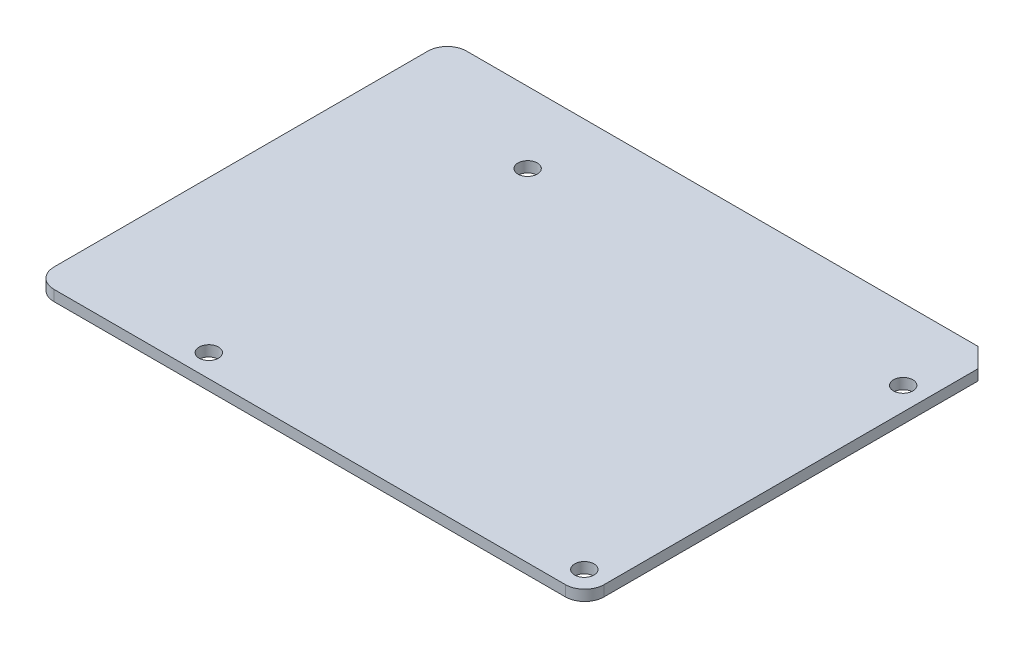
SolidWorks part; units mm, degrees
ref_plane "Front Plane" through (0, 0, 0) normal (0, 0, 1) x (1, 0, 0)
ref_plane "Top Plane" through (0, 0, 0) normal (0, 1, 0) x (1, 0, 0)
ref_plane "Right Plane" through (0, 0, 0) normal (1, 0, 0) x (0, 0, -1)
sketch "Sketch2" plane through (0, 0, 0) normal (0, 1, 0) x (1, 0, 0)
  line L1 (-42.57, -31.93) -> (42.57, -31.93)
  line L2 (-42.57, -31.93) -> (-42.57, 31.93)
  line L3 (-42.57, 31.93) -> (42.57, 31.93)
  line L4 (42.57, -31.93) -> (42.57, 31.93)
  line L5 (-42.57, -31.93) -> (42.57, 31.93) construction
  line L6 (-42.57, 31.93) -> (42.57, -31.93) construction
  line L7 (39.01, -28.43) -> (-19.11, -28.43) construction
  line L8 (39.01, -28.43) -> (39.01, 20.91) construction
  line L9 (39.01, 20.91) -> (-19.11, 20.91) construction
  line L10 (-19.11, -28.43) -> (-19.11, 20.91) construction
  line L11 (39.01, -28.43) -> (-19.11, 20.91) construction
  line L12 (39.01, 20.91) -> (-19.11, -28.43) construction
  circle A0 centre (-19.11, 20.91) radius 1.5
  circle A1 centre (39.01, 20.91) radius 1.5
  circle A2 centre (39.01, -28.43) radius 1.5
  circle A3 centre (-19.11, -28.43) radius 1.5
  point P0 (0, 0)
  point P6 (9.95, -3.76)
  dimension "D7" = 3
  dimension "D1" = 3.56
  dimension "D2" = 3.5
  dimension "D3" = 23.46
  dimension "D4" = 11.02
  dimension "D5" = 85.14
  dimension "D6" = 63.86
extrude "Boss-Extrude1" add sketch "Sketch2" along normal mid plane 1.65
fillet "Fillet1" radius 3 3 edges at (-42.57, 0, -31.93) (-42.57, 0, 31.93) (42.57, 0, 31.93)
chamfer "Chamfer1" distance 3 angle 45 1 edges at (42.57, 0, -31.93)
sketch "Sketch3" plane through (0, 0.825, 0) normal (0, 1, 0) x (1, 0, 0)
  line L0 (42.57, -28.93) -> (42.57, 28.93) construction
  line L1 (42.57, -18.93) -> (29.57, -18.93)
  line L2 (42.57, -18.93) -> (42.57, -8.93)
  line L3 (42.57, -8.93) -> (29.57, -8.93)
  line L4 (29.57, -18.93) -> (29.57, -8.93)
  line L5 (-39.57, -31.93) -> (39.57, -31.93) construction
  line L6 (29.57, -2.93) -> (29.57, 2.07)
  line L7 (42.57, -2.93) -> (37.57, -2.93)
  line L8 (42.57, -2.93) -> (42.57, 2.07)
  line L9 (42.57, 2.07) -> (37.57, 2.07)
  line L10 (37.57, -2.93) -> (37.57, 2.07)
  line L11 (34.57, 2.07) -> (29.57, 2.07)
  line L12 (34.57, -2.93) -> (34.57, 2.07)
  line L13 (34.57, -2.93) -> (29.57, -2.93)
  line L15 (26.57, 2.07) -> (16.57, 2.07)
  line L16 (26.57, -2.93) -> (26.57, 2.07)
  line L17 (26.57, -2.93) -> (16.57, -2.93)
  line L18 (16.57, 2.07) -> (16.57, -2.93)
  dimension "D1" = 13
  dimension "D2" = 13
  dimension "D3" = 10
  dimension "D4" = 6
  dimension "D5" = 5
  dimension "D6" = 5
  dimension "D8" = 3
  dimension "D7" = 3
  dimension "D9" = 5
  dimension "D10" = 5
  dimension "D11" = 5
  dimension "D12" = 10
